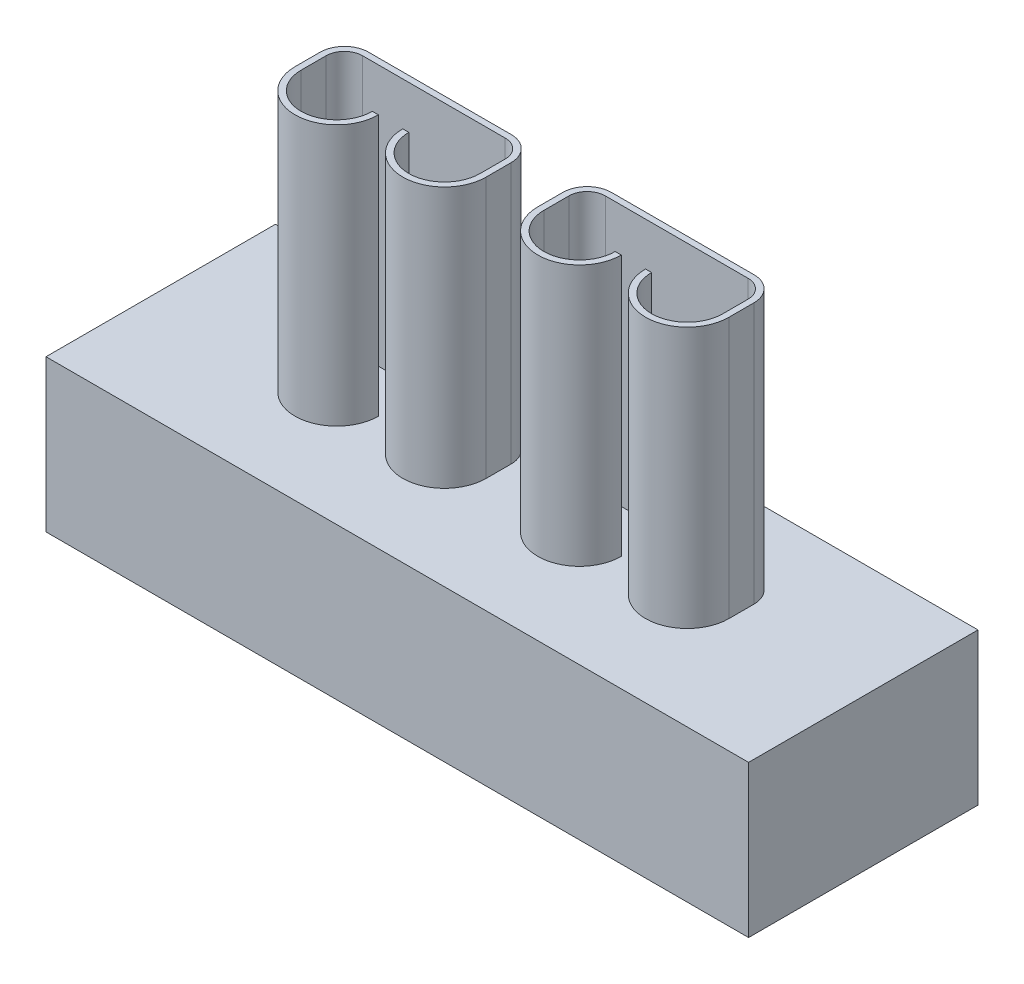
SolidWorks part; units mm, degrees
ref_plane "Front" through (0, 0, 0) normal (0, 0, 1) x (1, 0, 0)
ref_plane "Top" through (0, 0, 0) normal (0, 1, 0) x (1, 0, 0)
ref_plane "Right" through (0, 0, 0) normal (1, 0, 0) x (0, 0, -1)
sketch "Sketch1" plane through (0, 0, 0) normal (0, 1, 0) x (1, 0, 0)
  line L1 (-7.35, -2.4) -> (7.35, -2.4)
  line L2 (-7.35, -2.4) -> (-7.35, 2.4)
  line L3 (-7.35, 2.4) -> (7.35, 2.4)
  line L4 (7.35, -2.4) -> (7.35, 2.4)
  line L5 (-7.35, -2.4) -> (7.35, 2.4) construction
  line L6 (-7.35, 2.4) -> (7.35, -2.4) construction
  point P0 (0, 0)
  dimension "D1" = 14.7
  dimension "D2" = 4.8
extrude "Boss-Extrude1" add sketch "Sketch1" along normal blind 3.175
sketch "Sketch2" plane through (0, 3.175, 0) normal (0, 1, 0) x (1, 0, 0)
  line L0 (-4.032, 1.032) -> (-1.048, 1.032)
  line L1 (-0.54, 0.524) -> (-0.54, 0)
  line L2 (-4.54, 0.524) -> (-4.54, 0)
  line L3 (-2.54, 1.032) -> (-2.54, -2.4) construction
  line L4 (-7.35, -2.4) -> (7.35, -2.4) construction
  line L5 (0, 2.4) -> (0, -2.4) construction
  line L6 (7.35, 2.4) -> (-7.35, 2.4) construction
  line L7 (2.54, 1.032) -> (2.54, -2.4) construction
  line L8 (4.54, 0.524) -> (4.54, 0)
  line L9 (0.54, 0.524) -> (0.54, 0)
  line L10 (4.032, 1.032) -> (1.048, 1.032)
  line L11 (-3.667, 1.032) -> (-3.667, -0.873) construction
  line L12 (-3.667, 0) -> (0, 0) construction
  line L13 (-4.413, 0.524) -> (-4.413, 0)
  line L14 (-4.032, 0.905) -> (-1.048, 0.905)
  line L15 (-0.667, 0.524) -> (-0.667, 0)
  line L16 (-2.921, 0) -> (-2.794, 0)
  line L17 (-2.286, 0) -> (-2.159, 0)
  line L18 (4.413, 0.524) -> (4.413, 0)
  line L19 (4.032, 0.905) -> (1.048, 0.905)
  line L20 (0.667, 0.524) -> (0.667, 0)
  line L21 (2.159, 0) -> (2.286, 0)
  line L22 (2.794, 0) -> (2.921, 0)
  arc A0 (-4.54, 0) -> (-2.794, 0) centre (-3.667, 0) ccw
  arc A1 (-0.54, 0) -> (-2.286, 0) centre (-1.413, 0) cw
  arc A2 (0.54, 0) -> (2.286, 0) centre (1.413, 0) ccw
  arc A3 (4.54, 0) -> (2.794, 0) centre (3.667, 0) cw
  arc A4 (4.54, 0.524) -> (4.032, 1.032) centre (4.032, 0.524) ccw
  arc A5 (0.54, 0.524) -> (1.048, 1.032) centre (1.048, 0.524) cw
  arc A6 (-1.048, 1.032) -> (-0.54, 0.524) centre (-1.048, 0.524) cw
  arc A7 (-4.032, 1.032) -> (-4.54, 0.524) centre (-4.032, 0.524) ccw
  arc A8 (-4.413, 0) -> (-2.921, 0) centre (-3.667, 0) ccw
  arc A9 (-4.032, 0.905) -> (-4.413, 0.524) centre (-4.032, 0.524) ccw
  arc A10 (-1.048, 0.905) -> (-0.667, 0.524) centre (-1.048, 0.524) cw
  arc A11 (-0.667, 0) -> (-2.159, 0) centre (-1.413, 0) cw
  arc A12 (4.413, 0) -> (2.921, 0) centre (3.667, 0) cw
  arc A13 (4.413, 0.524) -> (4.032, 0.905) centre (4.032, 0.524) ccw
  arc A14 (0.667, 0.524) -> (1.048, 0.905) centre (1.048, 0.524) cw
  arc A15 (0.667, 0) -> (2.159, 0) centre (1.413, 0) ccw
  point P8 (-3.667, -0.873)
  point P27 (3.667, -0.873)
  point P30 (4.54, 1.032)
  point P33 (0.54, 1.032)
  point P36 (-0.54, 1.032)
  point P39 (-4.54, 1.032)
  dimension "D5" = 0.508
  dimension "D1" = 4
  dimension "D2" = 1.905
  dimension "D3" = 0.508
  dimension "D4" = 5.08
  dimension "D6" = 0.127
  dimension "D7" = 0.127
extrude "Boss-Extrude2" add sketch "Sketch2" along normal blind 5.461
